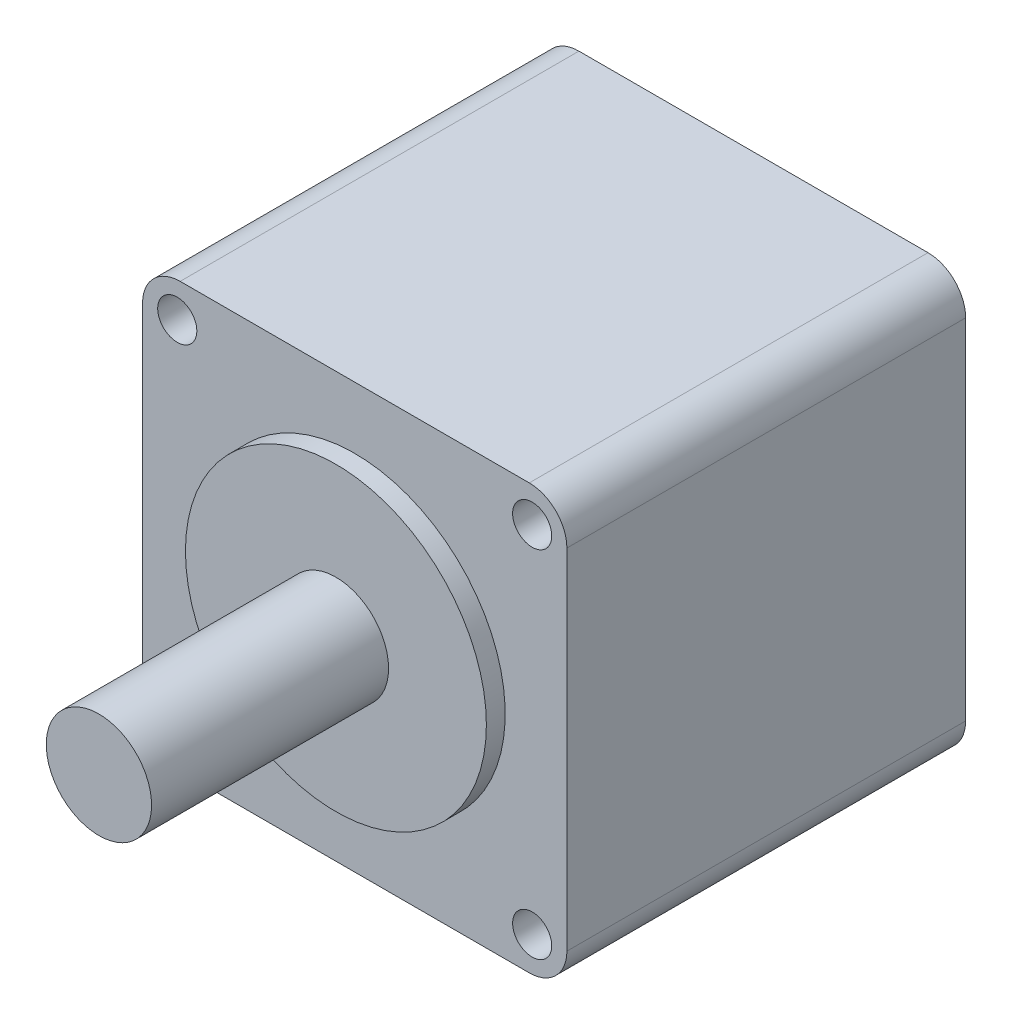
SolidWorks part; units mm, degrees
ref_plane "前视基准面" through (0, 0, 0) normal (0, 0, 1) x (1, 0, 0)
ref_plane "上视基准面" through (0, 0, 0) normal (0, 1, 0) x (1, 0, 0)
ref_plane "右视基准面" through (0, 0, 0) normal (1, 0, 0) x (0, 0, -1)
sketch "草图1" plane through (0, 0, 0) normal (0, 0, 1) x (1, 0, 0)
  line L1 (0, 0) -> (56.4, 0)
  line L2 (0, 0) -> (0, 56.4)
  line L3 (0, 56.4) -> (56.4, 56.4)
  line L4 (56.4, 0) -> (56.4, 56.4)
  dimension "D1" = 56.4
  dimension "D2" = 56.4
extrude "凸台-拉伸1" add sketch "草图1" along normal blind 53
sketch "草图2" plane through (0, 0, 53) normal (0, 0, 1) x (1, 0, 0)
  line L0 (28.2, 56.4) -> (28.2, 0) construction
  line L1 (56.4, 56.4) -> (0, 56.4) construction
  line L2 (0, 0) -> (56.4, 0) construction
  line L3 (28.2, 0) -> (28.2, 28.2) construction
  circle A0 centre (28.2, 28.2) radius 20
  dimension "D1" = 40
extrude "凸台-拉伸2" add sketch "草图2" along normal blind 2.5
sketch "草图3" plane through (0, 0, 55.5) normal (0, 0, 1) x (1, 0, 0)
  circle A0 centre (28.2, 28.2) radius 7
  dimension "D1" = 14
extrude "凸台-拉伸3" add sketch "草图3" along normal blind 31.5
fillet "圆角1" radius 5 4 edges at (0, 0, 26.5) (0, 56.4, 26.5) (56.4, 0, 26.5) (56.4, 56.4, 26.5)
sketch "草图4" plane through (0, 0, 53) normal (0, 0, 1) x (1, 0, 0)
  line L0 (28.2, 56.4) -> (28.2, 0) construction
  line L1 (51.4, 56.4) -> (5, 56.4) construction
  line L2 (5, 0) -> (51.4, 0) construction
  line L3 (28.2, 0) -> (28.2, 28.2) construction
  line L4 (28.2, 28.2) -> (63.8009, 28.2) construction
  circle A0 centre (4.615, 51.785) radius 2.6
  circle A1 centre (51.785, 51.785) radius 2.6
  circle A2 centre (51.785, 4.615) radius 2.6
  circle A3 centre (4.615, 4.615) radius 2.6
  dimension "D1" = 5.2
  dimension "D2" = 47.17
  dimension "D3" = 47.17
extrude "切除-拉伸1" cut sketch "草图4" against normal through all
